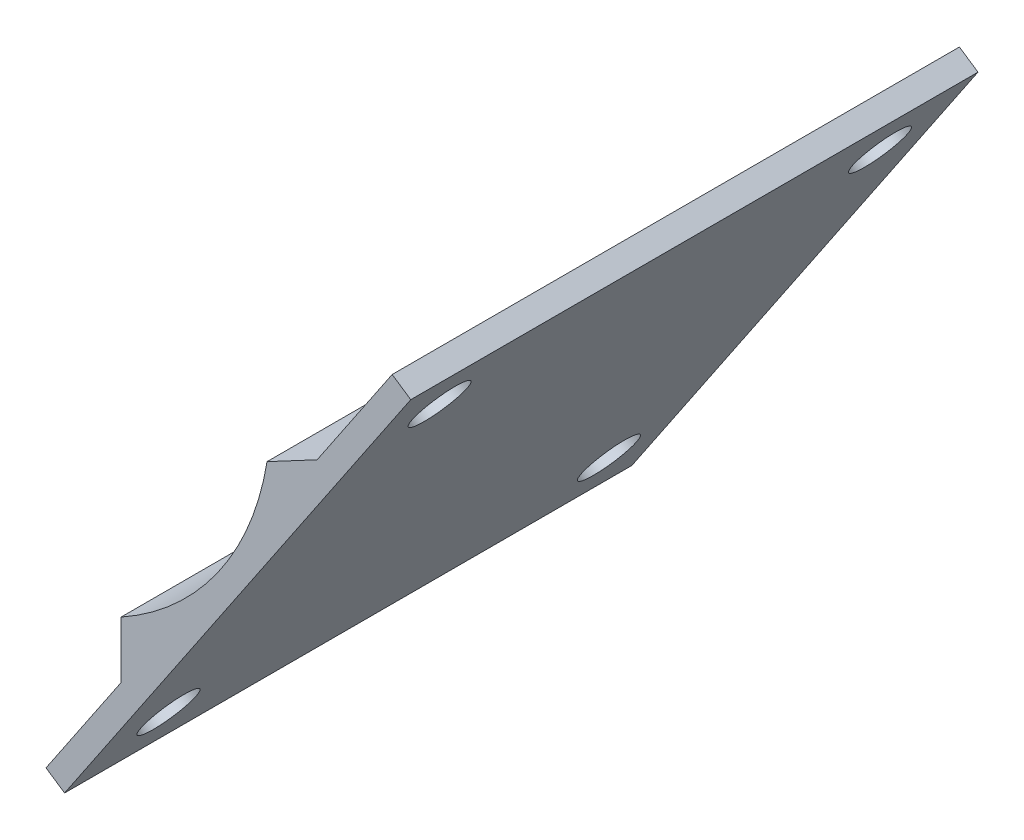
SolidWorks part; units mm, degrees
ref_plane "Front Plane" through (0, 0, 0) normal (0, 0, 1) x (1, 0, 0)
ref_plane "Top Plane" through (0, 0, 0) normal (0, 1, 0) x (1, 0, 0)
ref_plane "Right Plane" through (0, 0, 0) normal (1, 0, 0) x (0, 0, -1)
sketch "Sketch1" plane through (0, 0, 0) normal (0, 0, 1) x (1, 0, 0)
  line L0 (19.2454, -3.1409) -> (22.599, -1.3573)
  line L1 (22.599, -1.3573) -> (27.6282, 6.1065)
  line L2 (27.6282, 6.1065) -> (28.8721, 5.2683)
  line L3 (28.8721, 5.2683) -> (5.6823, -29.148)
  line L4 (5.6823, -29.148) -> (4.4383, -28.3098)
  line L5 (4.4383, -28.3098) -> (9.4675, -20.846)
  line L6 (9.4675, -20.846) -> (9.4675, -17.0475)
  arc A0 (9.4675, -17.0475) -> (19.2454, -3.1409) centre (0, 0) ccw
  dimension "D1" = 19.5
  dimension "D2" = 17
  dimension "D3" = 41.5
  dimension "D4" = 9
  dimension "D5" = 9
  dimension "D6" = 1.5
extrude "Boss-Extrude1" add sketch "Sketch1" along normal blind 38
sketch "Sketch2" plane through (16.1715, -10.8964, 0) normal (-0.8293, 0.5588, 0) x (0, 0, 1)
  line L0 (0, 20.5026) -> (0, 11.5026) construction
  line L1 (0, -11.9974) -> (0, -20.9974) construction
  circle A0 centre (4.05, 16.0026) radius 1.85
  circle A1 centre (33.55, 16.0026) radius 1.85
  circle A2 centre (4.05, -16.4974) radius 1.85
  circle A3 centre (33.55, -16.4974) radius 1.85
  dimension "D1" = 3.7
  dimension "D2" = 29.5
  dimension "D3" = 4.05
  dimension "D4" = 4.05
  dimension "D5" = 29.5
extrude "Cut-Extrude1" cut sketch "Sketch2" against normal through all
